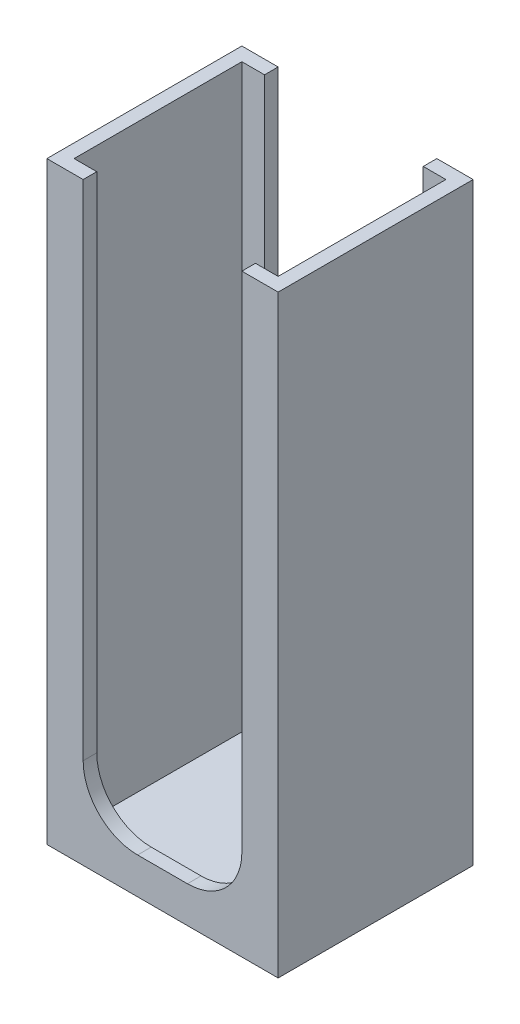
SolidWorks part; units mm, degrees
ref_plane "Front Plane" through (0, 0, 0) normal (0, 0, 1) x (1, 0, 0)
ref_plane "Top Plane" through (0, 0, 0) normal (0, 1, 0) x (1, 0, 0)
ref_plane "Right Plane" through (0, 0, 0) normal (1, 0, 0) x (0, 0, -1)
sketch "Sketch1" plane through (0, 0, 0) normal (0, 1, 0) x (1, 0, 0)
  line L1 (-66.5961, -35.7932) -> (-41.0961, -35.7932)
  line L2 (-66.5961, -35.7932) -> (-66.5961, -14.2932)
  line L3 (-66.5961, -14.2932) -> (-41.0961, -14.2932)
  line L4 (-41.0961, -35.7932) -> (-41.0961, -14.2932)
  dimension "D1" = 25.5
  dimension "D2" = 21.5
extrude "Boss-Extrude1" add sketch "Sketch1" along normal blind 65.5
sketch "Sketch2" plane through (0, 65.5, 0) normal (0, 1, 0) x (1, 0, 0)
  line L0 (-66.5961, -14.2932) -> (-66.5961, -35.7932) construction
  line L1 (-65.0961, -15.7932) -> (-42.5961, -15.7932)
  line L2 (-65.0961, -15.7932) -> (-65.0961, -34.2932)
  line L3 (-65.0961, -34.2932) -> (-42.5961, -34.2932)
  line L4 (-42.5961, -15.7932) -> (-42.5961, -34.2932)
  line L5 (-41.0961, -14.2932) -> (-66.5961, -14.2932) construction
  line L6 (-41.0961, -35.7932) -> (-41.0961, -14.2932) construction
  line L7 (-66.5961, -35.7932) -> (-41.0961, -35.7932) construction
  dimension "D1" = 1.5
  dimension "D2" = 1.5
  dimension "D3" = 1.5
  dimension "D4" = 1.5
extrude "Cut-Extrude1" cut sketch "Sketch2" against normal blind 64
sketch "Sketch5" plane through (0, 0, 35.7932) normal (0, 0, 1) x (1, 0, 0)
  line L0 (-66.5961, 65.5) -> (-41.0961, 65.5) construction
  line L1 (-45.0961, 65.5) -> (-62.5961, 65.5)
  line L2 (-45.0961, 65.5) -> (-45.0961, 10)
  line L3 (-51.0961, 4) -> (-56.5961, 4)
  line L4 (-62.5961, 65.5) -> (-62.5961, 10)
  line L5 (-41.0961, 65.5) -> (-41.0961, 0) construction
  line L6 (-66.5961, 65.5) -> (-66.5961, 0) construction
  line L7 (-66.5961, 0) -> (-41.0961, 0) construction
  arc A0 (-56.5961, 4) -> (-62.5961, 10) centre (-56.5961, 10) cw
  arc A1 (-45.0961, 10) -> (-51.0961, 4) centre (-51.0961, 10) cw
  dimension "D4" = 6
  dimension "D1" = 4
  dimension "D2" = 4
  dimension "D3" = 4
extrude "Cut-Extrude2" cut sketch "Sketch5" against normal blind 21.5
